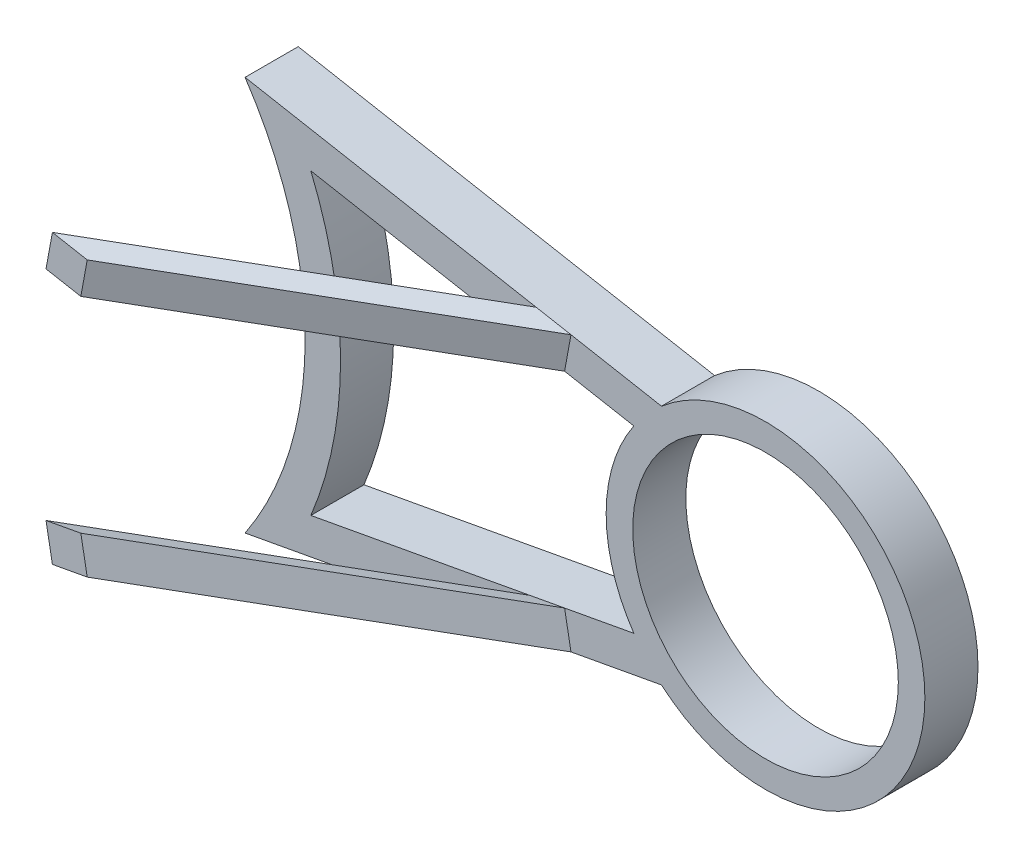
SolidWorks part; units mm, degrees
ref_plane "Front Plane" through (0, 0, 0) normal (0, 0, 1) x (1, 0, 0)
ref_plane "Top Plane" through (0, 0, 0) normal (0, 1, 0) x (1, 0, 0)
ref_plane "Right Plane" through (0, 0, 0) normal (1, 0, 0) x (0, 0, -1)
ref_plane "Plane1" through (0, 0, 10859.4574) normal (0, 0, 1) x (1, 0, 0)
sketch "Sketch2" plane through (0, 0, 10859.4574) normal (0, 0, 1) x (1, 0, 0)
  line L0 (4595.9655, 3982.3097) -> (3420.1429, 4198.6727)
  line L1 (2589.7722, 3641.4613) -> (5577.4251, 3641.4613) construction
  line L2 (4517.9819, 3894.9805) -> (3605.872, 4062.8178)
  line L3 (4595.9655, 3300.613) -> (3420.1429, 3084.2499)
  line L4 (4517.9819, 3387.9421) -> (3605.872, 3220.1048)
  line L6 (4577.8683, 3398.9618) -> (3402.0457, 3182.5988) construction
  line L7 (4577.8683, 3883.9608) -> (3402.0457, 4100.3239) construction
  circle A0 centre (2589.7722, 3641.4613) radius 1000 construction
  arc A1 (3420.1429, 3084.2499) -> (3420.1429, 4198.6727) centre (2589.7722, 3641.4613) ccw
  circle A2 centre (4889.7722, 3641.4613) radius 375
  arc A3 (4517.9819, 3894.9805) -> (4517.9819, 3387.9421) centre (4889.7722, 3641.4613) ccw
  arc A4 (3605.872, 3220.1048) -> (3605.872, 4062.8178) centre (2589.7722, 3641.4613) ccw
  arc A5 (4595.9655, 3300.613) -> (4595.9655, 3982.3097) centre (4889.7722, 3641.4613) ccw
  circle A6 centre (2589.7722, 3641.4613) radius 1100 construction
  circle A7 centre (2589.7722, 3641.4613) radius 1000 construction
  point P10 (3546.077, 3933.833)
  point P18 (3689.7722, 3641.4613)
  dimension "D3" = 750
  dimension "D4" = 450
  dimension "D1" = 100
  dimension "D5" = 2300
  dimension "D2" = 100
extrude "Extrude1" add sketch "Sketch2" along normal blind 150
ref_plane "Plane2" through (0, 3641.4613, 0) normal (0, 1, 0) x (-1, 0, 0)
sketch "Sketch4" plane through (0, 3641.4613, 0) normal (0, 1, 0) x (-1, 0, 0)
  line L0 (-4595.9655, 11009.4574) -> (-2977.2431, 11944.0272)
  line L1 (-4595.9655, 11009.4574) -> (-3420.1429, 11009.4574) construction
  dimension "D1" = 30
sketch "Sketch3" plane through (0, 0, 11009.4574) normal (0, 0, 1) x (1, 0, 0)
  line L0 (4340.4848, 4029.3207) -> (4242.136, 4047.4178)
  line L1 (4340.4848, 4029.3207) -> (4322.3876, 3930.9718)
  line L2 (4242.136, 4047.4178) -> (4224.0388, 3949.069)
  line L3 (4322.3876, 3930.9718) -> (4224.0388, 3949.069)
  line L4 (4595.9655, 3982.3097) -> (3420.1429, 4198.6727) construction
  line L6 (4889.7722, 3641.4613) -> (2589.7722, 3641.4613) construction
  line L7 (4322.3876, 3351.9508) -> (4224.0388, 3333.8537)
  line L8 (4242.136, 3235.5048) -> (4224.0388, 3333.8537)
  line L9 (4340.4848, 3253.602) -> (4322.3876, 3351.9508)
  line L10 (4340.4848, 3253.602) -> (4242.136, 3235.5048)
  dimension "D1" = 100
  dimension "D2" = 100
extrude "Extrude2" add sketch "Sketch3" along direction (-0.866, 0, 0.5) on the side of the normal blind 1000
